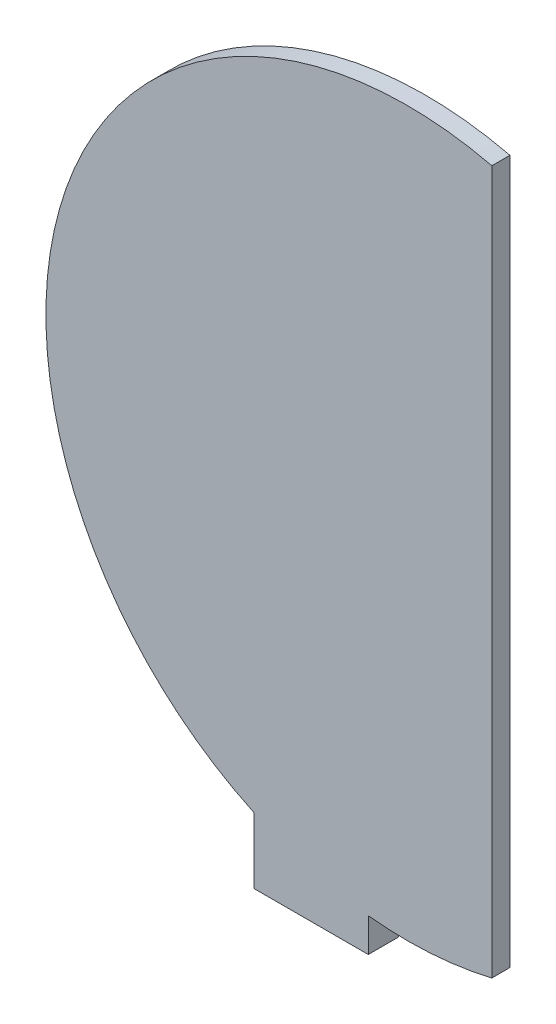
SolidWorks part; units mm, degrees
ref_plane "Front Plane" through (0, 0, 0) normal (0, 0, 1) x (1, 0, 0)
ref_plane "Top Plane" through (0, 0, 0) normal (0, 1, 0) x (1, 0, 0)
ref_plane "Right Plane" through (0, 0, 0) normal (1, 0, 0) x (0, 0, -1)
sketch "Sketch1" plane through (0, 0, 0) normal (0, 0, 1) x (1, 0, 0)
  line L0 (11.4193, 73.4545) -> (11.4193, -43.2421)
  arc A0 (11.4193, 73.4545) -> (11.4193, -43.2421) centre (-2.5618, 15.1062) ccw
  dimension "D1" = 60
  dimension "D2" = 11.4193
  dimension "D3" = 2.5618
  dimension "D4" = 15.1062
extrude "Boss-Extrude1" add sketch "Sketch1" along normal blind 3
sketch "Sketch2" plane through (0, 0, 3) normal (0, 0, 1) x (1, 0, 0)
  line L0 (-28.0807, -50.1211) -> (-28.0807, -25.777)
  line L1 (-28.0807, -50.1211) -> (-9.0807, -50.1211)
  line L2 (-28.0807, -25.777) -> (-9.0807, -25.777)
  line L3 (-9.0807, -50.1211) -> (-9.0807, -25.777)
  dimension "D1" = 20.5
  dimension "D2" = 24.3441
  dimension "D3" = 19
  dimension "D4" = 99.2315
extrude "Boss-Extrude2" add sketch "Sketch2" against normal blind 5
